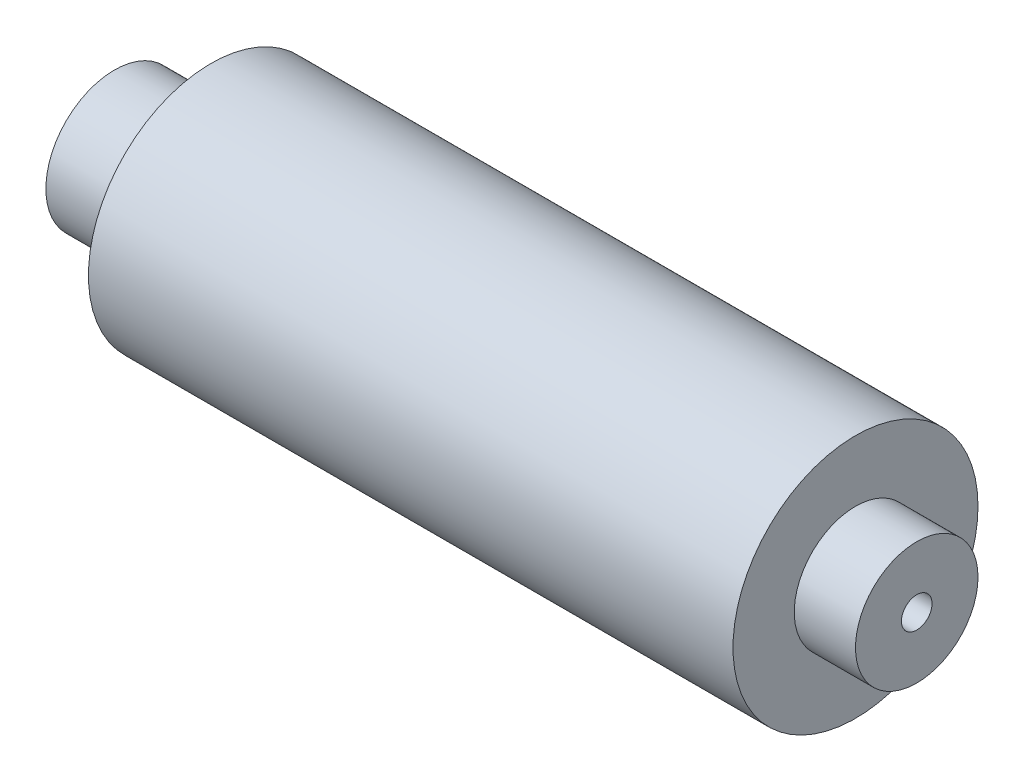
SolidWorks part; units mm, degrees
ref_plane "Front Plane" through (0, 0, 0) normal (0, 0, 1) x (1, 0, 0)
ref_plane "Top Plane" through (0, 0, 0) normal (0, 1, 0) x (1, 0, 0)
ref_plane "Right Plane" through (0, 0, 0) normal (1, 0, 0) x (0, 0, -1)
sketch "Sketch2" plane through (0, 0, 0) normal (0, 1, 0) x (1, 0, 0)
  line L0 (0, 2.3812) -> (0, 3.556)
  line L1 (0, 3.556) -> (5, 3.556)
  line L2 (5, 3.556) -> (5, 6.35)
  line L3 (5, 6.35) -> (38.4125, 6.35)
  line L5 (41.5875, 0.7938) -> (11.5875, 0.7938)
  line L6 (11.5875, 0.7938) -> (10, 2.3812)
  line L7 (10, 2.3812) -> (0, 2.3812)
  line L8 (0, 0) -> (-6.6729, 0) construction
  line L9 (38.4125, 6.35) -> (38.4125, 3.175)
  line L10 (38.4125, 3.175) -> (41.5875, 3.175)
  line L11 (41.5875, 3.175) -> (41.5875, 0.7938)
  dimension "D1" = 135
  dimension "D2" = 2.3813
  dimension "D3" = 0.7937
  dimension "D4" = 6.35
  dimension "D5" = 3.556
  dimension "D6" = 10
  dimension "D7" = 30
  dimension "D8" = 5
  dimension "D9" = 3.175
  dimension "D10" = 3.175
revolve "Revolve1" add sketch "Sketch2" angle 360 about L8
